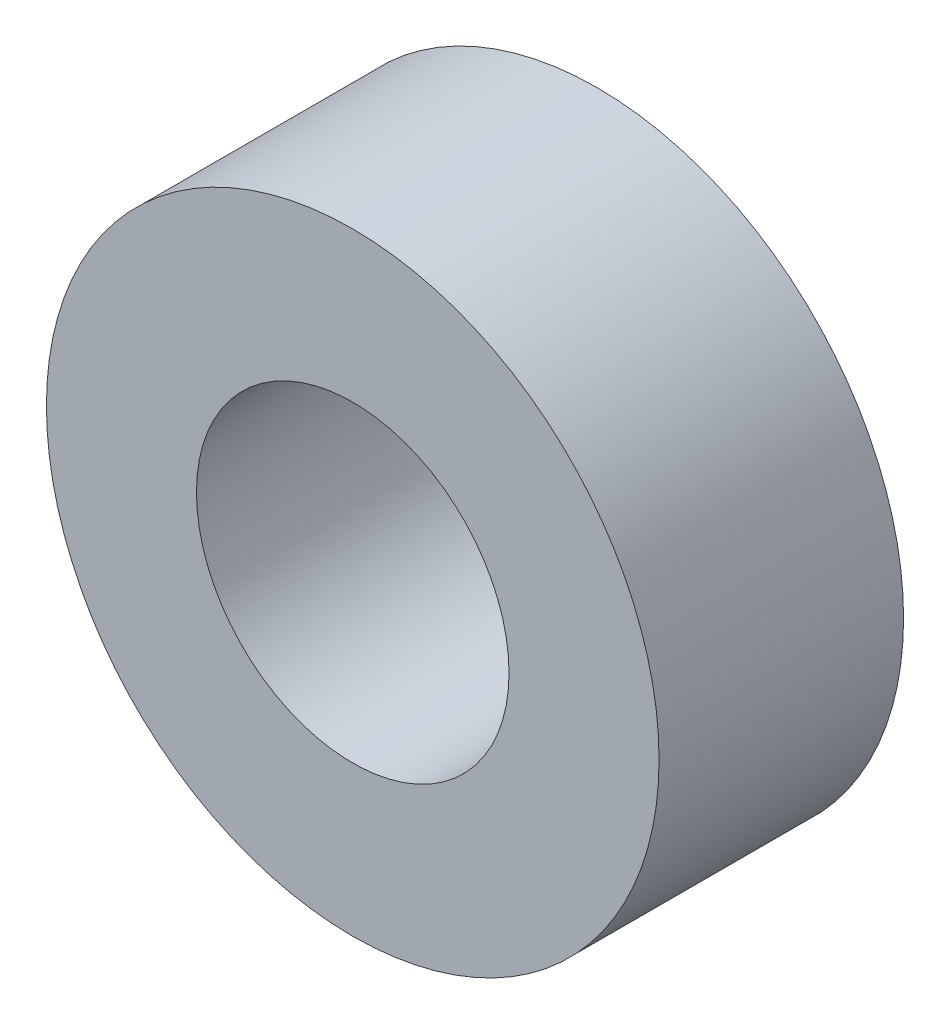
SolidWorks part; units mm, degrees
material "Tungsten"
ref_plane "Front Plane" through (0, 0, 0) normal (0, 0, 1) x (1, 0, 0)
ref_plane "Top Plane" through (0, 0, 0) normal (0, 1, 0) x (1, 0, 0)
ref_plane "Right Plane" through (0, 0, 0) normal (1, 0, 0) x (0, 0, -1)
sketch "Sketch1" plane through (0, 0, 0) normal (0, 0, 1) x (1, 0, 0)
  circle A0 centre (0, 0) radius 9.525
  circle A1 centre (0, 0) radius 18.669
  dimension "D1" = 19.05
  dimension "D2" = 37.338
extrude "Boss-Extrude1" add sketch "Sketch1" along normal mid plane 14.9016
ref_point "Point1"
